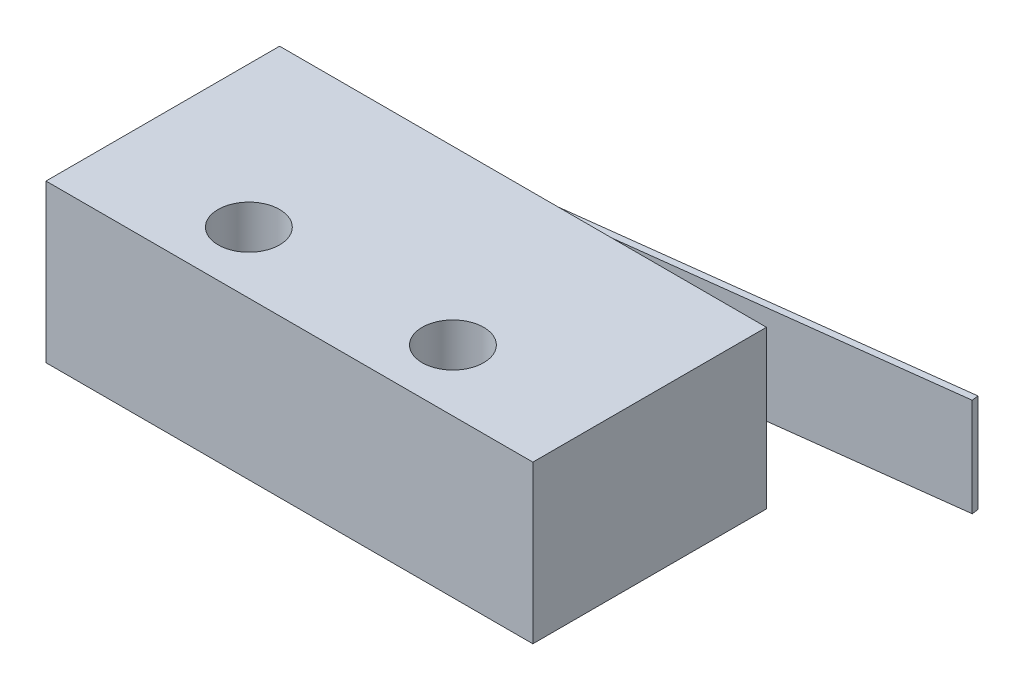
SolidWorks part; units mm, degrees
ref_plane "Front" through (0, 0, 0) normal (0, 0, 1) x (1, 0, 0)
ref_plane "Top" through (0, 0, 0) normal (0, 1, 0) x (1, 0, 0)
ref_plane "Right" through (0, 0, 0) normal (1, 0, 0) x (0, 0, -1)
sketch "草圖1" plane through (0, 0, 0) normal (0, 1, 0) x (1, 0, 0)
  line L1 (0, 0) -> (19.8, 0)
  line L2 (0, 0) -> (0, 9.5)
  line L3 (0, 9.5) -> (19.8, 9.5)
  line L4 (19.8, 0) -> (19.8, 9.5)
  dimension "D1" = 9.5
  dimension "D2" = 19.8
extrude "填料-伸長1" add sketch "草圖1" along normal blind 6.4
sketch "草圖2" plane through (0, 6.4, 0) normal (0, 1, 0) x (1, 0, 0)
  line L0 (5.75, 2.5) -> (14.05, 2.5) construction
  line L1 (0, 0) -> (19.8, 0) construction
  line L2 (9.9, 2.5) -> (9.9, 0) construction
  circle A0 centre (5.75, 2.5) radius 1.25
  circle A1 centre (14.05, 2.5) radius 1.25
  dimension "D1" = 2.5
  dimension "D2" = 2.5
  dimension "D3" = 2.5
  dimension "D4" = 8.3
extrude "除料-伸長1" cut sketch "草圖2" against normal blind 6.4
sketch "草圖3" plane through (0, 6.4, 0) normal (0, 1, 0) x (1, 0, 0)
  line L0 (2.645, 9.5) -> (25.3538, 12.3147)
  line L1 (2.645, 9.5) -> (2.6117, 9.7686)
  line L2 (25.3538, 12.3147) -> (25.3205, 12.5833)
  line L3 (2.6117, 9.7686) -> (25.3205, 12.5833)
  line L4 (19.8, 9.5) -> (0, 9.5) construction
extrude "填料-伸長2" add sketch "草圖3" against normal blind 4 from offset 1.2 separate body
